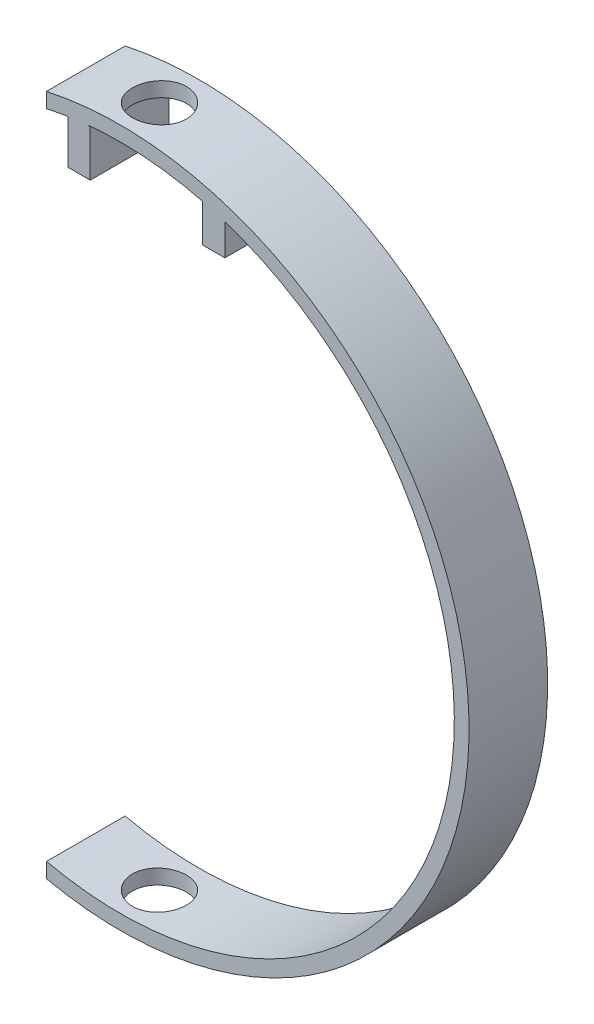
SolidWorks part; units mm, degrees
ref_plane "Front Plane" through (0, 0, 0) normal (0, 0, 1) x (1, 0, 0)
ref_plane "Top Plane" through (0, 0, 0) normal (0, 1, 0) x (1, 0, 0)
ref_plane "Right Plane" through (0, 0, 0) normal (1, 0, 0) x (0, 0, -1)
sketch "Sketch1" plane through (0, 0, 0) normal (0, 0, 1) x (1, 0, 0)
  line L6 (-15, 140.3974) -> (-15, 137.325)
  line L8 (-15, 4.675) -> (-15, 1.6026)
  arc A0 (0, 142) -> (0, 0) centre (0, 71) cw
  arc A2 (-15, 1.6026) -> (-15, 140.3974) centre (0, 71) ccw
  arc A3 (-15, 4.675) -> (-15, 137.325) centre (0, 71) ccw
  point P3 (0, 0)
  dimension "D1" = 71
  dimension "D2" = 3
  dimension "D3" = 15
  dimension "D4" = 15
  dimension "D5" = 142
extrude "Boss-Extrude1" add sketch "Sketch1" along normal blind 16 contours A3 L6 A2 L8
sketch "Sketch2" plane through (0, 0, 0) normal (0, 1, 0) x (1, 0, 0)
  line L3 (0, 0) -> (0, -16) construction
  line L4 (-15, -16) -> (71, -16) construction
  circle A0 centre (0, -8) radius 5.5
  point P6 (0, 0)
  point P7 (0, -8)
  dimension "D3" = 11
extrude "Cut-Extrude1" cut sketch "Sketch2" along normal through all
sketch "Sketch3" plane through (0, 0, 16) normal (0, 0, 1) x (1, 0, 0)
  line L0 (-6.1, 129.2) -> (-6.1, 138.6329)
  line L1 (-6.1, 129.2) -> (-10.6, 129.2)
  line L2 (-10.6, 129.2) -> (-10.6, 138.6329)
  line L3 (-10.6, 138.6329) -> (-6.1, 138.6329)
  line L4 (16.8, 129.2) -> (16.8, 136.892)
  line L5 (16.8, 129.2) -> (21.3, 129.2)
  line L6 (21.3, 129.2) -> (21.3, 136.892)
  line L7 (21.3, 136.892) -> (16.8, 136.892)
  arc A0 (-15, 4.675) -> (-15, 137.325) centre (0, 71) ccw construction
  dimension "D1" = 4.5
  dimension "D2" = 9.4329
  dimension "D3" = 4.5
extrude "Boss-Extrude2" add sketch "Sketch3" against normal up to surface (16 mm away) up to face at (27.25, 71, 0)
sketch "Sketch4" plane through (0, 129.2, 0) normal (0, -1, 0) x (1, 0, 0)
  circle A0 centre (19, 8) radius 0.9
  circle A1 centre (-8.3, 8) radius 0.9
  dimension "D1" = 1.8
  dimension "D2" = 1.8
extrude "Cut-Extrude2" cut sketch "Sketch4" against normal blind 8
